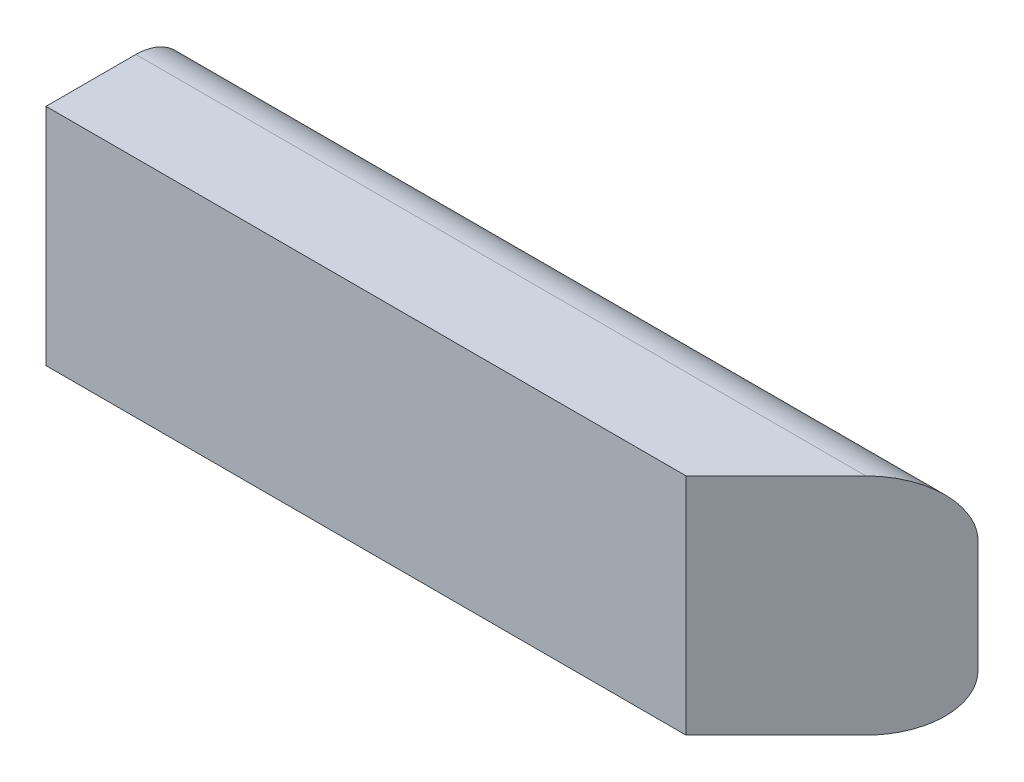
SolidWorks part; units mm, degrees
ref_plane "Front" through (0, 0, 0) normal (0, 0, 1) x (1, 0, 0)
ref_plane "Top" through (0, 0, 0) normal (0, 1, 0) x (1, 0, 0)
ref_plane "Right" through (0, 0, 0) normal (1, 0, 0) x (0, 0, -1)
sketch "Sketch1" plane through (0, 0, 0) normal (1, 0, 0) x (0, 0, -1)
  line L0 (0, 0) -> (0, 127) construction
  line L1 (0, 0) -> (31.75, 0)
  line L2 (31.75, 127) -> (0, 127)
  line L3 (63.5, 95.25) -> (63.5, 31.75)
  line L4 (0, 0) -> (-19.05, 0)
  line L5 (-19.05, 0) -> (-19.05, 127)
  line L6 (-19.05, 127) -> (0, 127)
  arc A0 (31.75, 0) -> (63.5, 31.75) centre (31.75, 31.75) ccw
  arc A1 (63.5, 95.25) -> (31.75, 127) centre (31.75, 95.25) ccw
  dimension "D2" = 63.5
  dimension "D1" = 19.05
extrude "Boss-Extrude1" add sketch "Sketch1" along normal blind 444.5
ref_plane "Mid_Plane" through (222.25, 0, 0) normal (1, 0, 0) x (0, 0, -1)
ref_plane "Plane1" through (190.5, 0, 190.5) normal (0.7071, 0, 0.7071) x (0, 1, 0)
sketch "Sketch2" plane through (190.5, 0, 190.5) normal (0.7071, 0, 0.7071) x (0, 1, 0)
  line L0 (31.75, -359.2102) -> (95.25, -359.2102) construction
  line L1 (205.1964, 31.0185) -> (-139.2061, 31.0185)
  line L2 (205.1964, 31.0185) -> (205.1964, -749.439)
  line L3 (205.1964, -749.439) -> (-139.2061, -749.439)
  line L4 (-139.2061, 31.0185) -> (-139.2061, -749.439)
  line L5 (205.1964, 31.0185) -> (-139.2061, -749.439) construction
  line L6 (205.1964, -749.439) -> (-139.2061, 31.0185) construction
  point P4 (32.9952, -359.2102)
extrude "Cut-Extrude1" cut sketch "Sketch2" along normal through all
